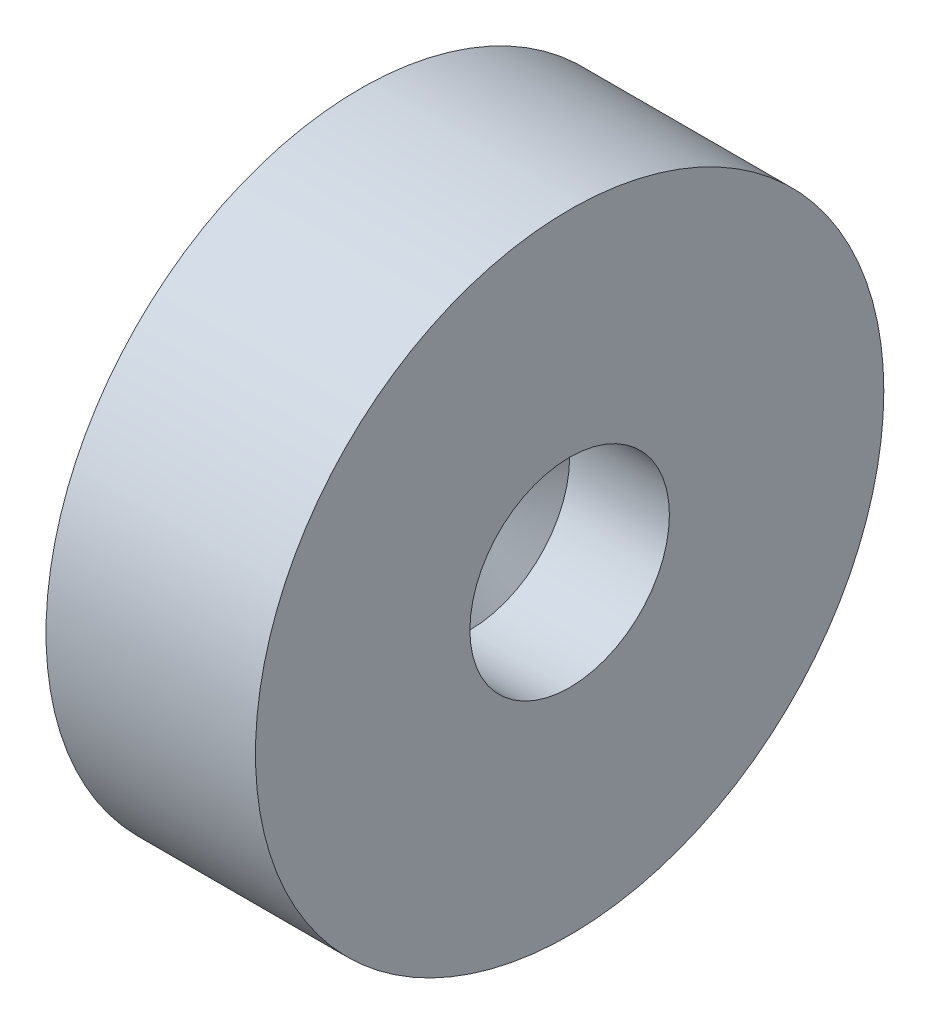
SolidWorks part; units mm, degrees
ref_plane "Front Plane" through (0, 0, 0) normal (0, 0, 1) x (1, 0, 0)
ref_plane "Top Plane" through (0, 0, 0) normal (0, 1, 0) x (1, 0, 0)
ref_plane "Right Plane" through (0, 0, 0) normal (1, 0, 0) x (0, 0, -1)
sketch "Sketch1" plane through (0, 0, 0) normal (1, 0, 0) x (0, 0, -1)
  circle A0 centre (0, 0) radius 15
  dimension "D1" = 30
extrude "Boss-Extrude1" add sketch "Sketch1" along normal blind 10 contours A0
sketch "Sketch2" plane through (0, 0, 0) normal (-1, 0, 0) x (0, 0, 1)
  line L1 (-7.5, -7.5) -> (7.5, -7.5)
  line L2 (-7.5, -7.5) -> (-7.5, 7.5)
  line L3 (-7.5, 7.5) -> (7.5, 7.5)
  line L4 (7.5, -7.5) -> (7.5, 7.5)
  line L5 (-7.5, -7.5) -> (7.5, 7.5) construction
  line L6 (-7.5, 7.5) -> (7.5, -7.5) construction
  point P0 (0, 0)
  dimension "D1" = 15
extrude "Cut-Extrude1" cut sketch "Sketch2" against normal blind 3
sketch "Sketch3" plane through (10, 0, 0) normal (1, 0, 0) x (0, 0, -1)
  circle A0 centre (0, 0) radius 4.7625
  dimension "D1" = 9.525
extrude "Cut-Extrude2" cut sketch "Sketch3" against normal blind 4.7625
sketch "Sketch4" plane through (0, 0, 0) normal (0, 0, 1) x (1, 0, 0)
  line L0 (5.2375, 4.7625) -> (3, 1.25)
  line L1 (3, 7.5) -> (3, -7.5) construction
  line L2 (3, 1.25) -> (3, 0)
  line L3 (3, 0) -> (5.2375, 0)
  line L4 (5.2375, -4.7625) -> (5.2375, 4.7625) construction
  line L5 (5.2375, 0) -> (5.2375, 4.7625)
  line L6 (5.2375, 0) -> (10.7132, 0) construction
  dimension "D1" = 9.525
  dimension "D2" = 2.5
revolve "Cut-Revolve1" cut sketch "Sketch4" angle 360 about L6
